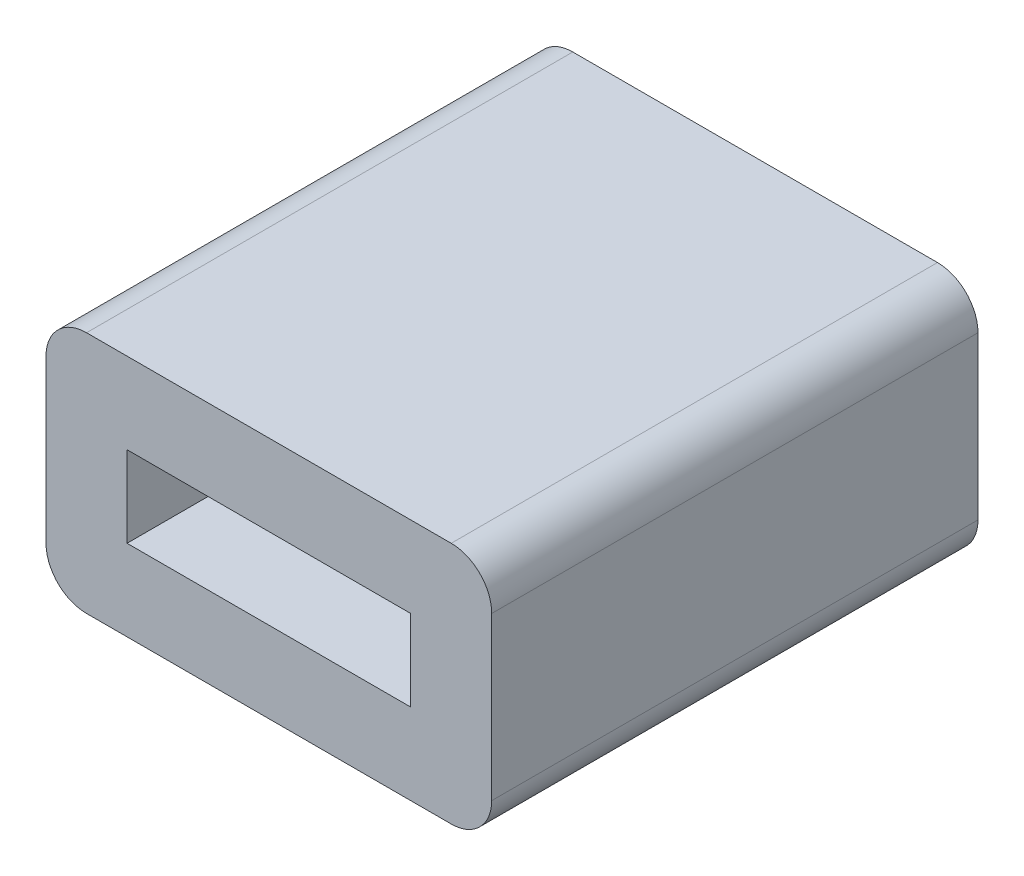
SolidWorks part; units mm, degrees
ref_plane "前视基准面" through (0, 0, 0) normal (0, 0, 1) x (1, 0, 0)
ref_plane "上视基准面" through (0, 0, 0) normal (0, 1, 0) x (1, 0, 0)
ref_plane "右视基准面" through (0, 0, 0) normal (1, 0, 0) x (0, 0, -1)
sketch "草图1" plane through (0, 0, 0) normal (0, 0, 1) x (1, 0, 0)
  line L1 (-3.5, -1) -> (3.5, -1)
  line L2 (-3.5, -1) -> (-3.5, 1)
  line L3 (-3.5, 1) -> (3.5, 1)
  line L4 (3.5, -1) -> (3.5, 1)
  line L5 (-3.5, -1) -> (3.5, 1) construction
  line L6 (-3.5, 1) -> (3.5, -1) construction
  line L7 (-4.5, -3) -> (4.5, -3)
  line L8 (-5.5, -2) -> (-5.5, 2)
  line L9 (-4.5, 3) -> (4.5, 3)
  line L10 (5.5, -2) -> (5.5, 2)
  line L11 (-5.5, -3) -> (5.5, 3) construction
  line L12 (-5.5, 3) -> (5.5, -3) construction
  arc A0 (-5.5, -2) -> (-4.5, -3) centre (-4.5, -2) ccw
  arc A1 (4.5, -3) -> (5.5, -2) centre (4.5, -2) ccw
  arc A2 (5.5, 2) -> (4.5, 3) centre (4.5, 2) ccw
  arc A3 (-5.5, 2) -> (-4.5, 3) centre (-4.5, 2) cw
  point P0 (0, 0)
  point P5 (0, 0)
  dimension "D1" = 7
  dimension "D2" = 2
  dimension "D3" = 11
  dimension "D5" = 1
  dimension "D4" = 6
extrude "凸台-拉伸1" add sketch "草图1" along normal blind 12
